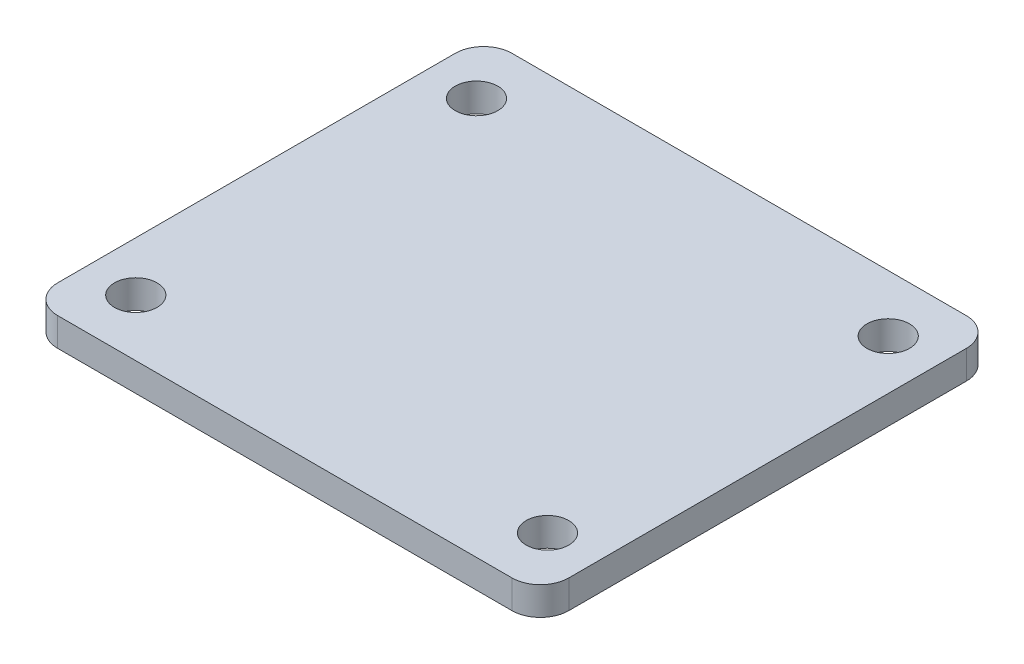
SolidWorks part; units mm, degrees
material "5052-H32"
ref_plane "Front Plane" through (0, 0, 0) normal (0, 0, 1) x (1, 0, 0)
ref_plane "Top Plane" through (0, 0, 0) normal (0, 1, 0) x (1, 0, 0)
ref_plane "Right Plane" through (0, 0, 0) normal (1, 0, 0) x (0, 0, -1)
sketch "Sketch1" plane through (0, 0, 0) normal (0, 1, 0) x (1, 0, 0)
  line L1 (57.15, 50.8) -> (-57.15, 50.8)
  line L2 (57.15, 50.8) -> (57.15, -50.8)
  line L3 (57.15, -50.8) -> (-57.15, -50.8)
  line L4 (-57.15, 50.8) -> (-57.15, -50.8)
  line L5 (57.15, 50.8) -> (-57.15, -50.8) construction
  line L6 (57.15, -50.8) -> (-57.15, 50.8) construction
  point P0 (0, 0)
  dimension "D1" = 101.6
  dimension "D2" = 114.3
extrude "Boss-Extrude1" add sketch "Sketch1" along normal blind 6.35
fillet "Fillet1" radius 6.35 4 edges at (57.15, 3.175, -50.8) (-57.15, 3.175, -50.8) (-57.15, 3.175, 50.8) (57.15, 3.175, 50.8)
hole_wizard "3/8 (0.375) Diameter Hole1" positions "3DSketch1" profile "Sketch2" hole size "3/8" standard "ANSI Inch" end condition through all
sketch3d "3DSketch1"
  line L0 (-50.8, 6.35, 50.8) -> (50.8, 6.35, 50.8) construction
  line L2 (57.15, 6.35, 44.45) -> (57.15, 6.35, -44.45) construction
  point P390 (46.0375, 6.35, 38.1)
  point P392 (-46.0375, 6.35, 38.1)
  point P394 (-46.0375, 6.35, -38.1)
  point P396 (46.0375, 6.35, -38.1)
  dimension "D1" = 76.2
  dimension "D3" = 12.7
  dimension "D2" = 92.075
  dimension "D4" = 11.1125
sketch "Sketch2" plane through (46.0375, 6.35, 38.1) normal (1, 0, 0) x (0, 0, 1)
  line L0 (0, 0) -> (0, 6.35)
  line L1 (0, 6.35) -> (4.7625, 6.35)
  line L2 (4.7625, 6.35) -> (4.7625, 0)
  line L5 (4.7625, 0) -> (0, 0)
  line L11 (0, -6.35) -> (0, 107.95) construction
  dimension "Thru Hole Dia." = 9.525
  dimension "Thru Hole Depth" = 6.35
